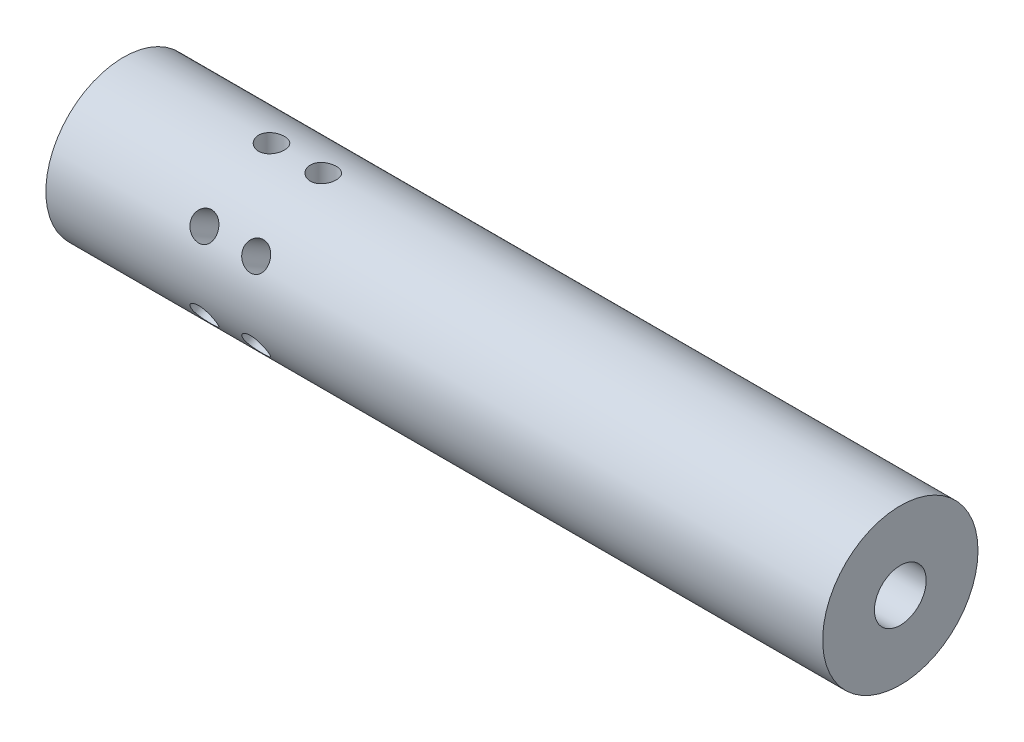
SolidWorks part; units mm, degrees
ref_plane "Front" through (0, 0, 0) normal (0, 0, 1) x (1, 0, 0)
ref_plane "Top" through (0, 0, 0) normal (0, 1, 0) x (1, 0, 0)
ref_plane "Right" through (0, 0, 0) normal (1, 0, 0) x (0, 0, -1)
sketch "Sketch1" plane through (0, 0, 0) normal (1, 0, 0) x (0, 0, -1)
  line L0 (0.5, 0) -> (1.5, 0) construction
  line L1 (0.5, 0) -> (1.5, 0) construction
  line L2 (1, 0) -> (1, 1.0672) construction
  circle A0 centre (0, 0) radius 1.5
  circle A1 centre (0, 0) radius 0.5
  point P4 (1.5, 0)
  point P5 (0.5, 0)
  dimension "OD" = 3
  dimension "ID" = 1
  dimension "Wall" = 1
  dimension "WallThk" = 1
extrude "Extrude1" add sketch "Sketch1" along normal mid plane 15
sketch "Sketch2" plane through (0, 0, 0) normal (0, 0, 1) x (1, 0, 0)
  line L0 (-7.5, 0) -> (7.5, 0) construction
  line L1 (-7.5, 1.5) -> (-7.5, -1.5) construction
  line L2 (7.5, -1.5) -> (7.5, 1.5) construction
sketch "Sketch3" plane through (0, 0, 0) normal (0, 1, 0) x (1, 0, 0)
  circle A0 centre (-4.6428, 0) radius 0.25
  dimension "D1" = 0.5
extrude "Cut-Extrude1" cut sketch "Sketch3" against normal blind 10
pattern_linear "LPattern1" count 2 spacing 1 along (1, 0, 0) of "Cut-Extrude1"
pattern_circular "CirPattern1" count 6 over 360 about axis through (7.5, 0, 0) along (-1, 0, 0) of "LPattern1", "Cut-Extrude1"
